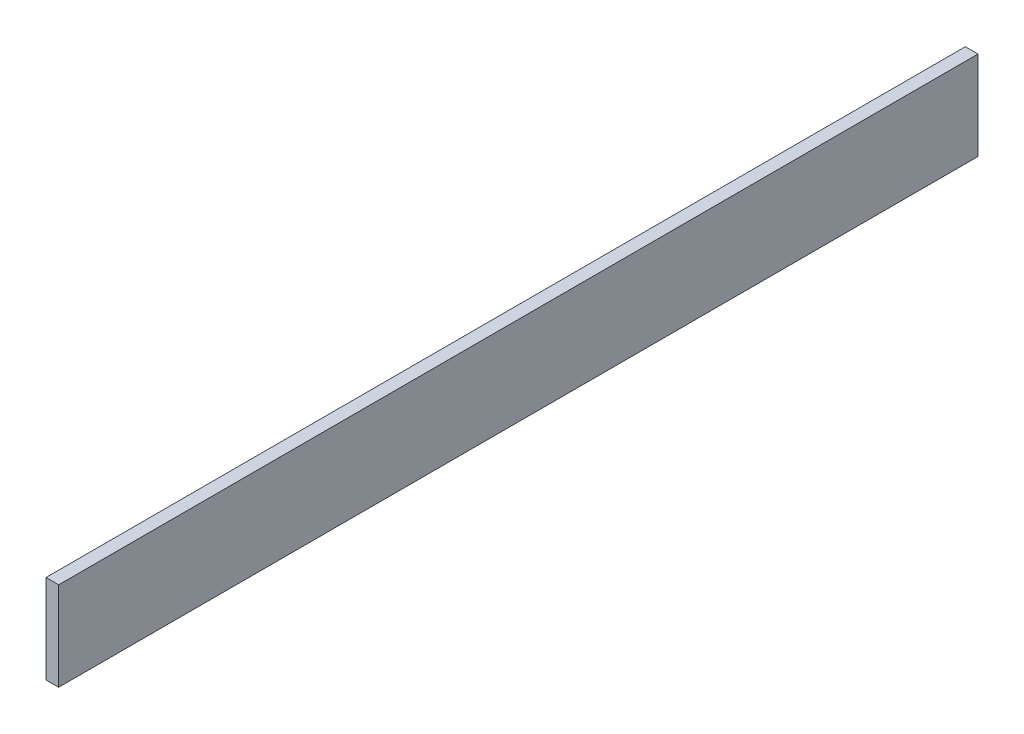
SolidWorks part; units mm, degrees
ref_plane "Front Plane" through (0, 0, 0) normal (0, 0, 1) x (1, 0, 0)
ref_plane "Top Plane" through (0, 0, 0) normal (0, 1, 0) x (1, 0, 0)
ref_plane "Right Plane" through (0, 0, 0) normal (1, 0, 0) x (0, 0, -1)
sketch "Sketch1" plane through (0, 0, 0) normal (0, 1, 0) x (1, 0, 0)
  line L1 (-5, -362.5) -> (5, -362.5)
  line L2 (-5, -362.5) -> (-5, 362.5)
  line L3 (-5, 362.5) -> (5, 362.5)
  line L4 (5, -362.5) -> (5, 362.5)
  line L5 (-5, -362.5) -> (5, 362.5) construction
  line L6 (-5, 362.5) -> (5, -362.5) construction
  point P0 (0, 0)
  dimension "D1" = 10
  dimension "D2" = 725
extrude "Boss-Extrude1" add sketch "Sketch1" along normal blind 70 contours L2 L3 L4 L1
